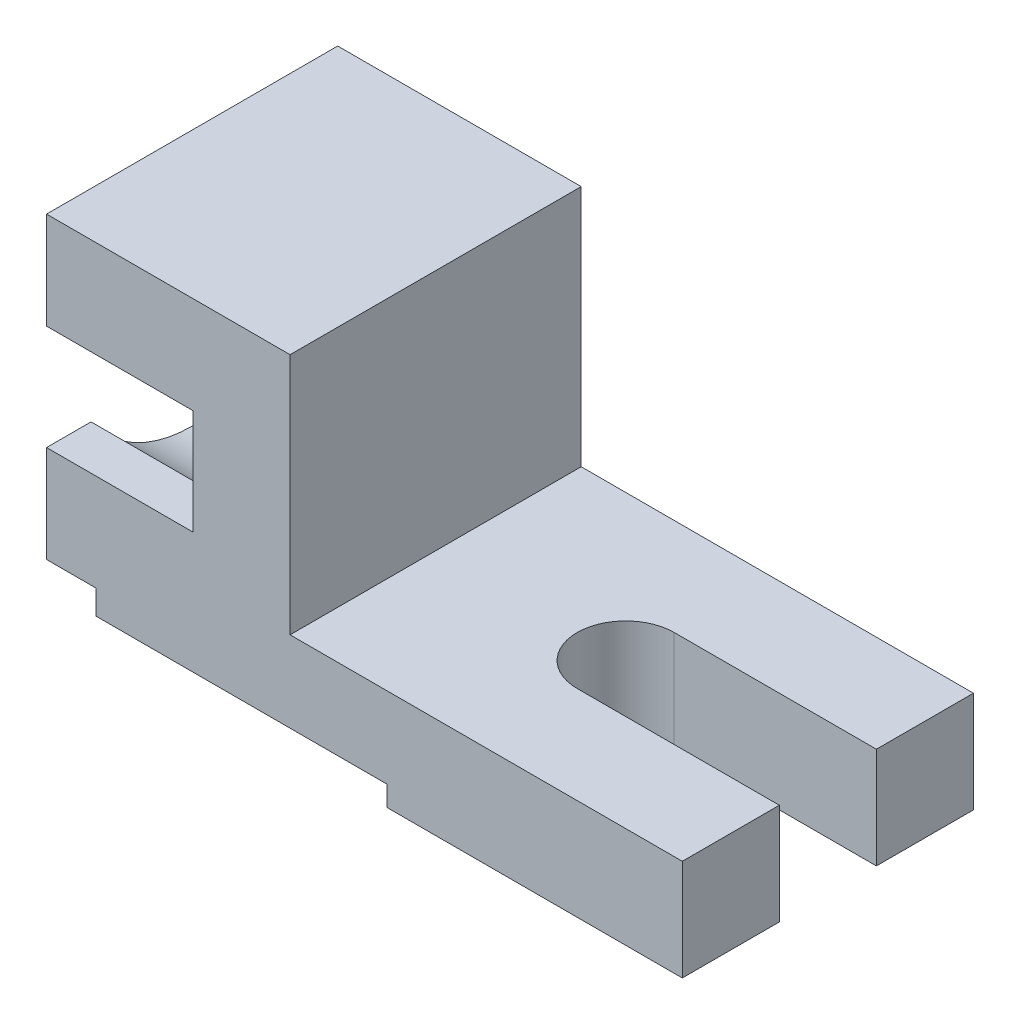
SolidWorks part; units mm, degrees
ref_plane "Front Plane" through (0, 0, 0) normal (0, 0, 1) x (1, 0, 0)
ref_plane "Top Plane" through (0, 0, 0) normal (0, 1, 0) x (1, 0, 0)
ref_plane "Right Plane" through (0, 0, 0) normal (1, 0, 0) x (0, 0, -1)
sketch "Sketch7" plane through (0, 0, 0) normal (0, 0, 1) x (1, 0, 0)
  line L0 (-85.7778, 17.7778) -> (-13.7778, 17.7778)
  line L1 (-13.7778, 17.7778) -> (-13.7778, 12.7778)
  line L2 (-13.7778, 12.7778) -> (59.2222, 12.7778)
  line L3 (59.2222, 12.7778) -> (59.2222, 37.7778)
  line L4 (59.2222, 37.7778) -> (-13.7778, 37.7778)
  line L5 (-13.7778, 37.7778) -> (-37.7778, 37.7778)
  line L6 (-37.7778, 37.7778) -> (-37.7778, 97.7778)
  line L7 (-37.7778, 97.7778) -> (-73.7778, 97.7778)
  line L8 (-73.7778, 97.7778) -> (-73.7778, 73.7778)
  line L9 (-73.7778, 73.7778) -> (-61.7778, 73.7778)
  line L10 (-85.7778, 17.7778) -> (-85.7778, 47.7778)
  line L11 (-85.7778, 47.7778) -> (-73.7778, 47.7778)
  line L12 (-73.7778, 47.7778) -> (-61.7778, 47.7778)
  line L13 (-61.7778, 47.7778) -> (-61.7778, 73.7778)
  dimension "D1" = 72
  dimension "D2" = 5
  dimension "D3" = 73
  dimension "D4" = 25
  dimension "D5" = 60
  dimension "D6" = 36
  dimension "D7" = 24
  dimension "D8" = 12
  dimension "D9" = 30
extrude "Boss-Extrude7" add sketch "Sketch7" against normal blind 72
sketch "Sketch8" plane through (0, 0, 0) normal (0, 0, 1) x (1, 0, 0)
  line L0 (59.2222, 37.7778) -> (9.2222, 37.7778) construction
  line L1 (59.2222, 37.7778) -> (-37.7778, 37.7778) construction
  dimension "D1" = 50
ref_plane "Plane1" through (0, 37.7778, 0) normal (0, 1, 0) x (1, 0, 0)
sketch "Sketch9" plane through (0, 37.7778, 0) normal (0, 1, 0) x (1, 0, 0)
  line L0 (59.2222, 0) -> (59.2222, 24) construction
  line L1 (59.2222, 72) -> (59.2222, 0) construction
  line L2 (59.2222, 24) -> (9.2222, 24)
  line L3 (59.2222, 24) -> (59.2222, 48)
  line L4 (59.2222, 48) -> (9.2222, 48)
  arc A0 (9.2222, 24) -> (9.2222, 48) centre (9.2222, 36) cw
  dimension "D1" = 24
  dimension "D2" = 24
extrude "Cut-Extrude4" cut sketch "Sketch9" against normal blind 72
ref_plane "Plane3" through (-62, 0, 0) normal (-1, 0, 0) x (0, 0, 1)
sketch "Sketch12" plane through (-62, 0, 0) normal (-1, 0, 0) x (0, 0, 1)
  line L0 (-72, 17.7778) -> (-72, 47.7778)
  line L1 (-72, 47.7778) -> (-61, 47.7778)
  line L2 (-72, 47.7778) -> (0, 47.7778) construction
  line L3 (-72, 17.7778) -> (-50, 17.7778)
  line L4 (-50, 17.7778) -> (-50, 23.7897)
  line L5 (-50, 23.7897) -> (0, 23.7897)
  line L6 (0, 23.7897) -> (0, 47.7778)
  line L7 (0, 47.7778) -> (-11, 47.7778)
  line L8 (-72, 97.7778) -> (-72, 73.7778)
  line L9 (-72, 73.7778) -> (-61, 73.7778)
  line L10 (-72, 73.7778) -> (0, 73.7778) construction
  line L11 (-72, 97.7778) -> (0, 97.7778)
  line L12 (0, 97.7778) -> (0, 73.7778)
  line L13 (0, 73.7778) -> (-11, 73.7778)
  line L14 (-72, 17.7778) -> (-72, 65.7778) construction
  line L15 (-72, 73.7778) -> (-72, 47.7778) construction
  line L16 (-72, 65.7778) -> (0, 65.7778) construction
  line L17 (0, 73.7778) -> (0, 47.7778) construction
  circle A0 centre (-36, 65.7778) radius 12
  arc A1 (-61, 73.7778) -> (-11, 73.7778) centre (-36, 57.1947) cw
  arc A2 (-61, 47.7778) -> (-11, 47.7778) centre (-36, 64.3609) ccw
  dimension "D5" = 24
  dimension "D6" = 30
  dimension "D7" = 30
  dimension "D1" = 11
  dimension "D2" = 22
  dimension "D3" = 11
  dimension "D4" = 48
extrude "Boss-Extrude8" add sketch "Sketch12" along normal blind 36 contours A2 L1 L0 L3 L4 L5 L6 L7 | L9 A1 L13 L12 L11 L8
sketch "Sketch13" plane through (-62, 0, 0) normal (-1, 0, 0) x (0, 0, 1)
  line L0 (-72, 47.7778) -> (-72, 73.7778)
  line L1 (-72, 73.7778) -> (-61, 73.7778)
  line L2 (-61, 73.7778) -> (-11, 73.7778) construction
  line L3 (-11, 73.7778) -> (0, 73.7778)
  line L4 (-72, 73.7778) -> (0, 73.7778) construction
  line L5 (0, 73.7778) -> (0, 47.7778)
  line L6 (0, 47.7778) -> (-11, 47.7778)
  line L7 (-61, 47.7778) -> (-72, 47.7778)
  line L8 (-72, 17.7778) -> (-72, 65.7778)
  line L9 (-61, 47.7778) -> (-11, 47.7778)
  line L10 (-61, 73.7778) -> (-43.4379, 73.7778)
  line L11 (-28.5621, 73.7778) -> (-11, 73.7778)
  line L12 (-61, 47.7778) -> (-11, 47.7778)
  line L13 (-43.4379, 73.7778) -> (-28.5621, 73.7778)
  line L14 (-61, 47.7778) -> (-11, 47.7778)
  arc A0 (-11, 73.7778) -> (-61, 73.7778) centre (-36, 57.1947) ccw construction
  arc A1 (-61, 73.7778) -> (-11, 73.7778) centre (-36, 57.1947) cw
  arc A2 (-11, 47.7778) -> (-61, 47.7778) centre (-36, 64.3609) cw
  dimension "D1" = 48
extrude "Cut-Extrude10" cut sketch "Sketch13" along normal blind 30 contours A2 L9 | A1 L10 L13 L11
sketch "Sketch17" plane through (-61.7778, 0, 0) normal (-1, 0, 0) x (0, 0, 1)
  line L0 (-73.0611, 16.5745) -> (-72, 64.5745) construction
  line L1 (-72, 73.7778) -> (-72, 47.7778) construction
  line L2 (-72, 64.5745) -> (-35.9327, 64.5745) construction
  circle A0 centre (-35.9327, 64.5745) radius 12
  dimension "D2" = 24
  dimension "D1" = 48
extrude "Cut-Extrude11" cut sketch "Sketch17" along normal blind 30 and the other way blind 1
